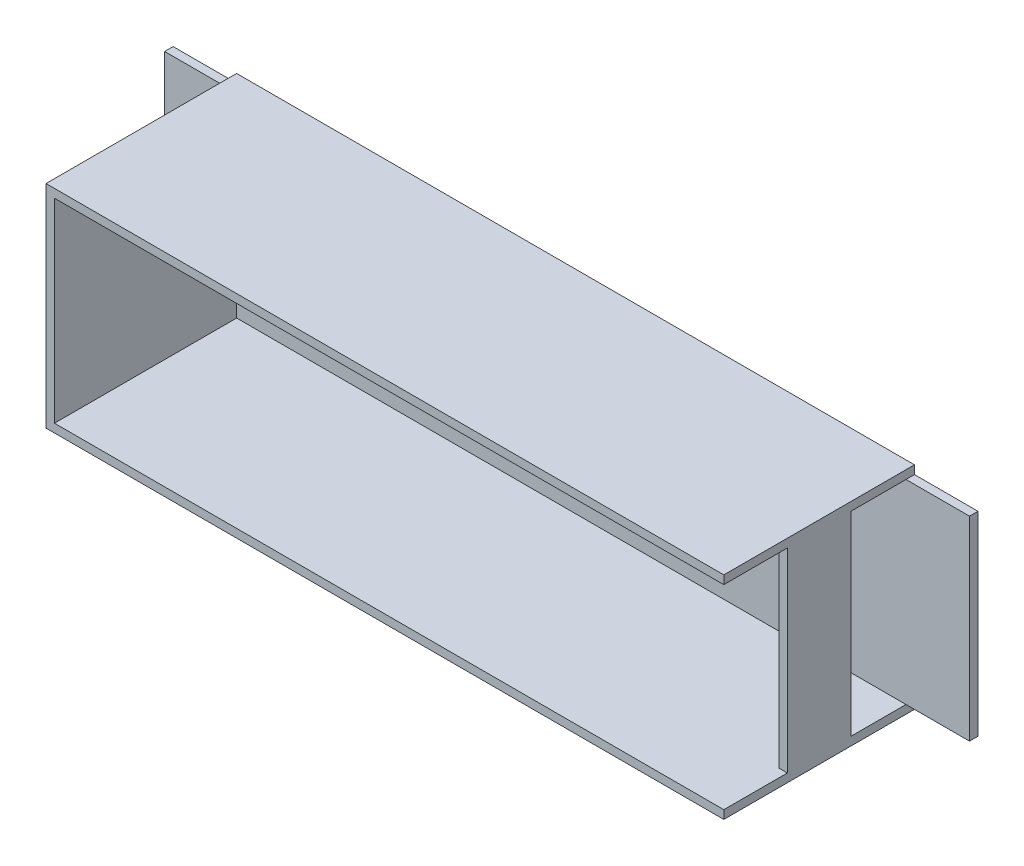
SolidWorks part; units mm, degrees
material "7075-O (SS)"
ref_plane "Plano frontal" through (0, 0, 0) normal (0, 0, 1) x (1, 0, 0)
ref_plane "Plano superior" through (0, 0, 0) normal (0, 1, 0) x (1, 0, 0)
ref_plane "Plano direito" through (0, 0, 0) normal (1, 0, 0) x (0, 0, -1)
sketch "Esboço1" plane through (0, 0, 0) normal (0, 0, 1) x (1, 0, 0)
  line L1 (-80, 25) -> (80, 25)
  line L2 (-80, 25) -> (-80, -25)
  line L3 (-80, -25) -> (80, -25)
  line L4 (80, 25) -> (80, -25)
  line L5 (-80, 25) -> (80, -25) construction
  line L6 (-80, -25) -> (80, 25) construction
  point P0 (0, 0)
  dimension "D1" = 160
  dimension "D2" = 50
extrude "Ressalto-extrusão1" add sketch "Esboço1" along normal blind 45
sketch "Esboço3" plane through (80, 0, 0) normal (1, 0, 0) x (0, 0, -1)
  line L0 (0, 23) -> (-2, 23)
  line L2 (-2, 23) -> (-2, -23)
  line L4 (-2, -23) -> (0, -23)
  line L5 (0, -23) -> (0, 23)
  point P5 (0, 0)
  point P7 (0, 0)
  dimension "D1" = 2
  dimension "D2" = 2
  dimension "D3" = 2
extrude "Ressalto-extrusão2" add sketch "Esboço3" along normal blind 15
sketch "Esboço9" plane through (0, 0, 45) normal (0, 0, 1) x (1, 0, 0)
  line L1 (-78, 23) -> (78, 23)
  line L2 (-78, 23) -> (-78, -23)
  line L3 (-78, -23) -> (78, -23)
  line L4 (78, 23) -> (78, -23)
  line L5 (-78, 23) -> (78, -23) construction
  line L6 (-78, -23) -> (78, 23) construction
  line L8 (80, 25) -> (-80, 25) construction
  line L9 (-80, 25) -> (-80, -25) construction
  point P0 (0, 0)
  dimension "D1" = 2
  dimension "D2" = 2
extrude "Corte-extrusão2" cut sketch "Esboço9" against normal blind 43
sketch "Esboço10" plane through (80, 0, 0) normal (1, 0, 0) x (0, 0, -1)
  line L0 (-45, 25) -> (0, 25) construction
  line L1 (-45, -23) -> (-30, -23)
  line L2 (-45, -23) -> (-45, 23)
  line L3 (-45, 23) -> (-30, 23)
  line L4 (-30, -23) -> (-30, 23)
  line L5 (-45, -25) -> (0, -25) construction
  line L6 (-45, -25) -> (-45, 25) construction
  line L7 (-2, 23) -> (-2, -23) construction
  line L8 (-2, -23) -> (-15, -23)
  line L9 (-2, -23) -> (-2, 23)
  line L10 (-2, 23) -> (-15, 23)
  line L11 (-15, -23) -> (-15, 23)
  dimension "D1" = 2
  dimension "D2" = 2
  dimension "D3" = 15
  dimension "D4" = 13
extrude "Corte-extrusão3" cut sketch "Esboço10" against normal up to next
sketch "Esboço11" plane through (-80, 0, 0) normal (-1, 0, 0) x (0, 0, 1)
  line L0 (0, 23) -> (2, 23)
  line L2 (2, 23) -> (2, -23)
  line L4 (2, -23) -> (0, -23)
  line L5 (0, -23) -> (0, 23)
  dimension "D1" = 2
  dimension "D2" = 2
  dimension "D3" = 2
extrude "Ressalto-extrusão6" add sketch "Esboço11" along normal blind 15
